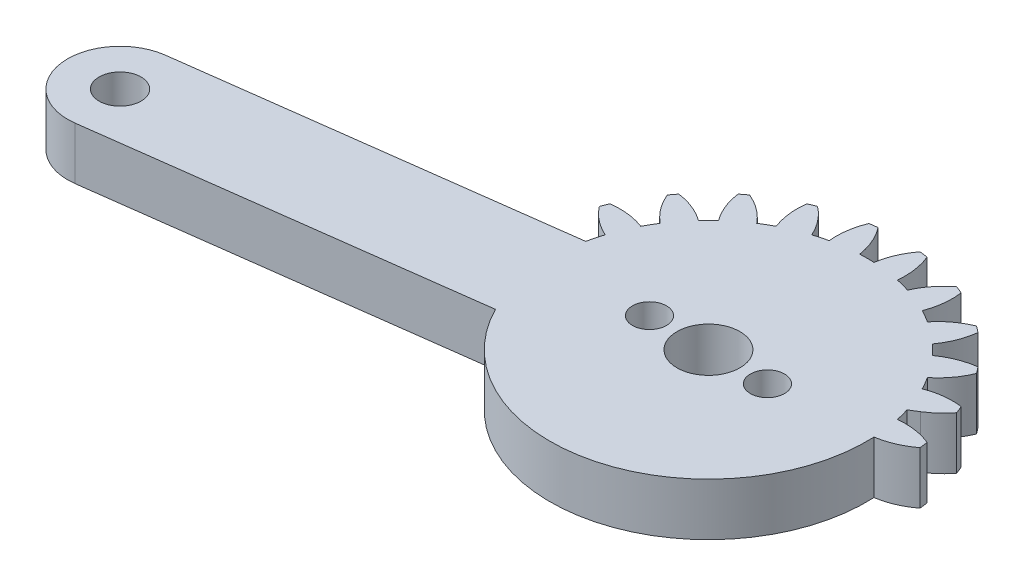
SolidWorks part; units mm, degrees
ref_plane "Front Plane" through (0, 0, 0) normal (0, 0, 1) x (1, 0, 0)
ref_plane "Top Plane" through (0, 0, 0) normal (0, 1, 0) x (1, 0, 0)
ref_plane "Right Plane" through (0, 0, 0) normal (1, 0, 0) x (0, 0, -1)
sketch "Sketch1" plane through (0, 0, 0) normal (0, 1, 0) x (1, 0, 0)
  line L0 (20.6437, 4) -> (2.0816, 4)
  line L1 (2.0816, -4) -> (20.6437, -4)
  arc A0 (2.0816, 4) -> (3.5217, 5.3071) centre (-0.7683, 8.5867) ccw
  arc A1 (3.5217, 5.3071) -> (3.2829, 5.8838) centre (-10.1063, 0) ccw
  arc A2 (3.2829, 5.8838) -> (0.6271, 5.5703) centre (2.5684, 0.5313) ccw
  arc A3 (0.6271, 5.5703) -> (0.0844, 6.5103) centre (-10.1063, 0) ccw
  arc A4 (0.0844, 6.5103) -> (1.6838, 8.6535) centre (-3.3089, 10.711) ccw
  arc A5 (1.6838, 8.6535) -> (1.3038, 9.1487) centre (-10.1063, 0) ccw
  arc A6 (1.3038, 9.1487) -> (-1.1803, 8.1585) centre (1.999, 3.7936) ccw
  arc A7 (-1.1803, 8.1585) -> (-1.9479, 8.926) centre (-10.1063, 0) ccw
  arc A8 (-1.9479, 8.926) -> (-0.9576, 11.4102) centre (-6.3127, 12.1053) ccw
  arc A9 (-0.9576, 11.4102) -> (-1.4528, 11.7901) centre (-10.1063, 0) ccw
  arc A10 (-1.4528, 11.7901) -> (-3.596, 10.1907) centre (0.6046, 6.7975) ccw
  arc A11 (-3.596, 10.1907) -> (-4.5361, 10.7334) centre (-10.1063, 0) ccw
  arc A12 (-4.5361, 10.7334) -> (-4.2225, 13.3892) centre (-9.5751, 12.6747) ccw
  arc A13 (-4.2225, 13.3892) -> (-4.7992, 13.6281) centre (-10.1063, 0) ccw
  arc A14 (-4.7992, 13.6281) -> (-6.4554, 11.5285) centre (-1.5196, 9.3381) ccw
  arc A15 (-6.4554, 11.5285) -> (-7.5039, 11.8094) centre (-10.1063, 0) ccw
  arc A16 (-7.5039, 11.8094) -> (-7.8884, 14.4558) centre (-12.8736, 12.3803) ccw
  arc A17 (-7.8884, 14.4558) -> (-8.5072, 14.5373) centre (-10.1063, 0) ccw
  arc A18 (-8.5072, 14.5373) -> (-9.5636, 12.0806) centre (-4.2291, 11.2423) ccw
  arc A19 (-9.5636, 12.0806) -> (-10.6491, 12.0806) centre (-10.1063, 0) ccw
  arc A20 (-10.6491, 12.0806) -> (-11.7054, 14.5373) centre (-15.9836, 11.2423) ccw
  arc A21 (-11.7054, 14.5373) -> (-12.3243, 14.4558) centre (-10.1063, 0) ccw
  arc A22 (-12.3243, 14.4558) -> (-12.7088, 11.8094) centre (-7.3391, 12.3803) ccw
  arc A23 (-12.7088, 11.8094) -> (-13.7573, 11.5285) centre (-10.1063, 0) ccw
  arc A24 (-13.7573, 11.5285) -> (-15.4135, 13.6281) centre (-18.6931, 9.3381) ccw
  arc A25 (-15.4135, 13.6281) -> (-15.9901, 13.3892) centre (-10.1063, 0) ccw
  arc A26 (-15.9901, 13.3892) -> (-15.6766, 10.7334) centre (-10.6376, 12.6747) ccw
  arc A27 (-15.6766, 10.7334) -> (-16.6166, 10.1907) centre (-10.1063, 0) ccw
  arc A28 (-16.6166, 10.1907) -> (-18.7599, 11.7901) centre (-20.8173, 6.7975) ccw
  arc A29 (-18.7599, 11.7901) -> (-19.255, 11.4102) centre (-10.1063, 0) ccw
  arc A30 (-19.255, 11.4102) -> (-18.2648, 8.926) centre (-13.9, 12.1053) ccw
  arc A31 (-18.2648, 8.926) -> (-19.0324, 8.1585) centre (-10.1063, 0) ccw
  arc A32 (-19.0324, 8.1585) -> (-21.5165, 9.1487) centre (-22.2117, 3.7936) ccw
  arc A33 (-21.5165, 9.1487) -> (-21.8965, 8.6535) centre (-10.1063, 0) ccw
  arc A34 (-21.8965, 8.6535) -> (-20.2971, 6.5103) centre (-16.9038, 10.711) ccw
  arc A35 (-20.2971, 6.5103) -> (-20.8398, 5.5703) centre (-10.1063, 0) ccw
  arc A36 (-20.8398, 5.5703) -> (-23.4956, 5.8838) centre (-22.7811, 0.5313) ccw
  arc A37 (-23.4956, 5.8838) -> (-23.7344, 5.3071) centre (-10.1063, 0) ccw
  arc A38 (-23.7344, 5.3071) -> (-21.6348, 3.6509) centre (-19.4444, 8.5867) ccw
  arc A39 (-21.6348, 3.6509) -> (-21.9157, 2.6025) centre (-10.1063, 0) ccw
  arc A40 (-21.9157, 2.6025) -> (-24.5622, 2.2179) centre (-22.4867, -2.7673) ccw
  arc A41 (-24.5622, 2.2179) -> (-24.6437, 1.5991) centre (-10.1063, 0) ccw
  arc A42 (-24.6437, 1.5991) -> (-22.1869, 0.5427) centre (-21.3486, 5.8773) ccw
  arc A43 (-22.1869, 0.5427) -> (-22.1869, -0.5427) centre (-10.1063, 0) ccw
  arc A44 (-22.1869, -0.5427) -> (-24.6437, -1.5991) centre (-21.3486, -5.8773) ccw
  arc A45 (-24.6437, -1.5991) -> (-24.5622, -2.2179) centre (-10.1063, 0) ccw
  arc A46 (-24.5622, -2.2179) -> (-21.9157, -2.6025) centre (-22.4867, 2.7673) ccw
  arc A47 (-21.9157, -2.6025) -> (-21.6348, -3.6509) centre (-10.1063, 0) ccw
  arc A48 (-21.6348, -3.6509) -> (-23.7344, -5.3071) centre (-19.4444, -8.5867) ccw
  arc A49 (-23.7344, -5.3071) -> (-23.4956, -5.8838) centre (-10.1063, 0) ccw
  arc A50 (-23.4956, -5.8838) -> (-20.8398, -5.5703) centre (-22.7811, -0.5313) ccw
  arc A51 (-20.8398, -5.5703) -> (-20.2971, -6.5103) centre (-10.1063, 0) ccw
  arc A52 (-20.2971, -6.5103) -> (-21.8965, -8.6535) centre (-16.9038, -10.711) ccw
  arc A53 (-21.8965, -8.6535) -> (-21.5165, -9.1487) centre (-10.1063, 0) ccw
  arc A54 (-21.5165, -9.1487) -> (-19.0324, -8.1585) centre (-22.2117, -3.7936) ccw
  arc A55 (-19.0324, -8.1585) -> (-18.2648, -8.926) centre (-10.1063, 0) ccw
  arc A56 (-18.2648, -8.926) -> (-19.255, -11.4102) centre (-13.9, -12.1053) ccw
  arc A57 (-19.255, -11.4102) -> (-18.7599, -11.7901) centre (-10.1063, 0) ccw
  arc A58 (-18.7599, -11.7901) -> (-16.6166, -10.1907) centre (-20.8173, -6.7975) ccw
  arc A59 (-16.6166, -10.1907) -> (-15.6766, -10.7334) centre (-10.1063, 0) ccw
  arc A60 (-15.6766, -10.7334) -> (-15.9901, -13.3892) centre (-10.6376, -12.6747) ccw
  arc A61 (-15.9901, -13.3892) -> (-15.4135, -13.6281) centre (-10.1063, 0) ccw
  arc A62 (-15.4135, -13.6281) -> (-13.7573, -11.5285) centre (-18.6931, -9.3381) ccw
  arc A63 (-13.7573, -11.5285) -> (-12.7088, -11.8094) centre (-10.1063, 0) ccw
  arc A64 (-12.7088, -11.8094) -> (-12.3243, -14.4558) centre (-7.3391, -12.3803) ccw
  arc A65 (-12.3243, -14.4558) -> (-11.7054, -14.5373) centre (-10.1063, 0) ccw
  arc A66 (-11.7054, -14.5373) -> (-10.6491, -12.0806) centre (-15.9836, -11.2423) ccw
  arc A67 (-10.6491, -12.0806) -> (-9.5636, -12.0806) centre (-10.1063, 0) ccw
  arc A68 (-9.5636, -12.0806) -> (-8.5072, -14.5373) centre (-4.2291, -11.2423) ccw
  arc A69 (-8.5072, -14.5373) -> (-7.8884, -14.4558) centre (-10.1063, 0) ccw
  arc A70 (-7.8884, -14.4558) -> (-7.5039, -11.8094) centre (-12.8736, -12.3803) ccw
  arc A71 (-7.5039, -11.8094) -> (-6.4554, -11.5285) centre (-10.1063, 0) ccw
  arc A72 (-6.4554, -11.5285) -> (-4.7992, -13.6281) centre (-1.5196, -9.3381) ccw
  arc A73 (-4.7992, -13.6281) -> (-4.2225, -13.3892) centre (-10.1063, 0) ccw
  arc A74 (-4.2225, -13.3892) -> (-4.5361, -10.7334) centre (-9.5751, -12.6747) ccw
  arc A75 (-4.5361, -10.7334) -> (-3.596, -10.1907) centre (-10.1063, 0) ccw
  arc A76 (-3.596, -10.1907) -> (-1.4528, -11.7901) centre (0.6046, -6.7975) ccw
  arc A77 (-1.4528, -11.7901) -> (-0.9576, -11.4102) centre (-10.1063, 0) ccw
  arc A78 (-0.9576, -11.4102) -> (-1.9479, -8.926) centre (-6.3127, -12.1053) ccw
  arc A79 (-1.9479, -8.926) -> (-1.1803, -8.1585) centre (-10.1063, 0) ccw
  arc A80 (-1.1803, -8.1585) -> (1.3038, -9.1487) centre (1.999, -3.7936) ccw
  arc A81 (1.3038, -9.1487) -> (1.6838, -8.6535) centre (-10.1063, 0) ccw
  arc A82 (1.6838, -8.6535) -> (0.0844, -6.5103) centre (-3.3089, -10.711) ccw
  arc A83 (0.0844, -6.5103) -> (0.6271, -5.5703) centre (-10.1063, 0) ccw
  arc A84 (0.6271, -5.5703) -> (3.2829, -5.8838) centre (2.5684, -0.5313) ccw
  arc A85 (3.2829, -5.8838) -> (3.5217, -5.3071) centre (-10.1063, 0) ccw
  arc A86 (3.5217, -5.3071) -> (2.0816, -4) centre (-0.7683, -8.5867) ccw
  arc A87 (20.6437, -4) -> (20.6437, 4) centre (20.6437, 0) ccw
  circle A88 centre (-10.1063, 0) radius 1.5
  circle A89 centre (20.6437, 0) radius 1.6
  dimension "D1" = 3
  dimension "D2" = 3.2
extrude "Boss-Extrude1" add sketch "Sketch1" along normal blind 4
sketch "Sketch3" plane through (0, 4, 0) normal (0, 1, 0) x (1, 0, 0)
  line L0 (-10.1063, 0) -> (-40.8563, 0) construction
  line L1 (-10.1063, 0) -> (-49.7641, -5.221)
  line L2 (-10.6284, 3.9658) -> (-50.2862, -1.2553)
  line L3 (-9.5842, -3.9658) -> (-49.242, -9.1868)
  line L4 (-10.1063, 0) -> (-4.5096, 13.5117) construction
  line L5 (-10.1063, 0) -> (-8.1974, 14.4999) construction
  circle A0 centre (-10.1063, 0) radius 1.5
  circle A1 centre (20.6437, 0) radius 1.6 construction
  circle A2 centre (20.6437, 0) radius 1.6
  circle A3 centre (-49.7641, -5.221) radius 1.6
  circle A4 centre (-49.7641, -5.221) radius 4
  circle A5 centre (-10.1063, 0) radius 4
  arc A6 (-4.2225, 13.3892) -> (-4.7992, 13.6281) centre (-10.1063, 0) ccw construction
  arc A7 (-7.8884, 14.4558) -> (-8.5072, 14.5373) centre (-10.1063, 0) ccw construction
  dimension "D2" = 3
  dimension "D5" = 3.2
  dimension "D6" = 8
  dimension "D7" = 8
  dimension "D1" = 40
  dimension "D4" = 7.5
extrude "Boss-Extrude2" add sketch "Sketch3" against normal blind 4
sketch "Sketch4" plane through (0, 4, 0) normal (0, 1, 0) x (1, 0, 0)
  line L0 (20.6437, 4) -> (2.0816, 4) construction
  line L1 (2.0816, -4) -> (20.6437, -4) construction
  line L2 (20.6437, 4) -> (2.0816, 4)
  line L3 (2.0816, -4) -> (20.6437, -4)
  line L4 (2.0816, 4) -> (1.4381, 3.6001)
  line L5 (-21.6245, -5.5509) -> (-20.8986, -5.4553)
  line L6 (-10.1063, 0) -> (0.0844, 6.5103) construction
  line L7 (-10.1063, 0) -> (1.9742, 0.5427) construction
  line L8 (-24.5755, 2.1296) -> (-50.2862, -1.2553)
  line L9 (-49.242, -9.1868) -> (-23.5312, -5.8019)
  line L10 (2.0816, -4) -> (20.6437, -4)
  line L11 (20.6437, 4) -> (2.0816, 4)
  line L12 (-21.9429, 2.4762) -> (-50.2862, -1.2553)
  line L13 (-49.242, -9.1868) -> (-21.6245, -5.5509)
  line L14 (2.0816, -4) -> (20.6437, -4)
  line L15 (20.6437, 4) -> (2.0816, 4)
  circle A0 centre (-10.1063, 0) radius 12.0927
  arc A1 (3.2829, 5.8838) -> (0.6271, 5.5703) centre (2.5684, 0.5313) ccw construction
  arc A2 (3.5217, 5.3071) -> (3.2829, 5.8838) centre (-10.1063, 0) ccw construction
  arc A3 (2.0816, 4) -> (3.5217, 5.3071) centre (-0.7683, 8.5867) ccw construction
  arc A4 (20.6437, -4) -> (20.6437, 4) centre (20.6437, 0) ccw construction
  arc A5 (3.5217, -5.3071) -> (2.0816, -4) centre (-0.7683, -8.5867) ccw construction
  arc A6 (3.2829, -5.8838) -> (3.5217, -5.3071) centre (-10.1063, 0) ccw construction
  arc A7 (0.6271, -5.5703) -> (3.2829, -5.8838) centre (2.5684, -0.5313) ccw construction
  arc A8 (3.2829, 5.8838) -> (0.6271, 5.5703) centre (2.5684, 0.5313) ccw
  arc A9 (3.5217, 5.3071) -> (3.2829, 5.8838) centre (-10.1063, 0) ccw
  arc A10 (2.0816, 4) -> (3.5217, 5.3071) centre (-0.7683, 8.5867) ccw
  arc A11 (20.6437, -4) -> (20.6437, 4) centre (20.6437, 0) ccw
  arc A12 (3.5217, -5.3071) -> (2.0816, -4) centre (-0.7683, -8.5867) ccw
  arc A13 (3.2829, -5.8838) -> (3.5217, -5.3071) centre (-10.1063, 0) ccw
  arc A14 (0.6271, -5.5703) -> (3.2829, -5.8838) centre (2.5684, -0.5313) ccw
  arc A15 (1.9742, 0.5427) -> (4.431, 1.5991) centre (1.1359, 5.8773) ccw
  arc A16 (4.3495, 2.2179) -> (1.7031, 2.6025) centre (2.274, -2.7673) ccw
  arc A17 (4.431, 1.5991) -> (4.3495, 2.2179) centre (-10.1063, 0) ccw
  arc A95 (-21.6348, 3.6509) -> (-21.9157, 2.6025) centre (-10.1063, 0) ccw
  arc A96 (-50.2862, -1.2553) -> (-49.242, -9.1868) centre (-49.7641, -5.221) ccw
  arc A97 (-20.2971, -6.5103) -> (-21.8965, -8.6535) centre (-16.9038, -10.711) ccw
  arc A98 (-21.8965, -8.6535) -> (-21.5165, -9.1487) centre (-10.1063, 0) ccw
  arc A99 (-21.5165, -9.1487) -> (-19.0324, -8.1585) centre (-22.2117, -3.7936) ccw
  arc A100 (-19.0324, -8.1585) -> (-18.2648, -8.926) centre (-10.1063, 0) ccw
  arc A101 (-18.2648, -8.926) -> (-19.255, -11.4102) centre (-13.9, -12.1053) ccw
  arc A102 (-19.255, -11.4102) -> (-18.7599, -11.7901) centre (-10.1063, 0) ccw
  arc A103 (-18.7599, -11.7901) -> (-16.6166, -10.1907) centre (-20.8173, -6.7975) ccw
  arc A104 (-16.6166, -10.1907) -> (-15.6766, -10.7334) centre (-10.1063, 0) ccw
  arc A105 (-15.6766, -10.7334) -> (-15.9901, -13.3892) centre (-10.6376, -12.6747) ccw
  arc A106 (-15.9901, -13.3892) -> (-15.4135, -13.6281) centre (-10.1063, 0) ccw
  arc A107 (-15.4135, -13.6281) -> (-13.7573, -11.5285) centre (-18.6931, -9.3381) ccw
  arc A108 (-13.7573, -11.5285) -> (-12.7088, -11.8094) centre (-10.1063, 0) ccw
  arc A109 (-12.7088, -11.8094) -> (-12.3243, -14.4558) centre (-7.3391, -12.3803) ccw
  arc A110 (-12.3243, -14.4558) -> (-11.7054, -14.5373) centre (-10.1063, 0) ccw
  arc A111 (-11.7054, -14.5373) -> (-10.6491, -12.0806) centre (-15.9836, -11.2423) ccw
  arc A112 (-10.6491, -12.0806) -> (-9.5636, -12.0806) centre (-10.1063, 0) ccw
  arc A113 (-9.5636, -12.0806) -> (-8.5072, -14.5373) centre (-4.2291, -11.2423) ccw
  arc A114 (-8.5072, -14.5373) -> (-7.8884, -14.4558) centre (-10.1063, 0) ccw
  arc A115 (-7.8884, -14.4558) -> (-7.5039, -11.8094) centre (-12.8736, -12.3803) ccw
  arc A116 (-7.5039, -11.8094) -> (-6.4554, -11.5285) centre (-10.1063, 0) ccw
  arc A117 (-6.4554, -11.5285) -> (-4.7992, -13.6281) centre (-1.5196, -9.3381) ccw
  arc A118 (-4.7992, -13.6281) -> (-4.2225, -13.3892) centre (-10.1063, 0) ccw
  arc A119 (-4.2225, -13.3892) -> (-4.5361, -10.7334) centre (-9.5751, -12.6747) ccw
  arc A120 (-4.5361, -10.7334) -> (-3.596, -10.1907) centre (-10.1063, 0) ccw
  arc A121 (-3.596, -10.1907) -> (-1.4528, -11.7901) centre (0.6046, -6.7975) ccw
  arc A122 (-1.4528, -11.7901) -> (-0.9576, -11.4102) centre (-10.1063, 0) ccw
  arc A123 (-0.9576, -11.4102) -> (-1.9479, -8.926) centre (-6.3127, -12.1053) ccw
  arc A124 (-1.9479, -8.926) -> (-1.1803, -8.1585) centre (-10.1063, 0) ccw
  arc A125 (-1.1803, -8.1585) -> (1.3038, -9.1487) centre (1.999, -3.7936) ccw
  arc A126 (1.3038, -9.1487) -> (1.6838, -8.6535) centre (-10.1063, 0) ccw
  arc A127 (1.6838, -8.6535) -> (0.0844, -6.5103) centre (-3.3089, -10.711) ccw
  arc A128 (0.0844, -6.5103) -> (0.6271, -5.5703) centre (-10.1063, 0) ccw
  arc A129 (0.6271, -5.5703) -> (3.2829, -5.8838) centre (2.5684, -0.5313) ccw
  arc A130 (3.2829, -5.8838) -> (3.5217, -5.3071) centre (-10.1063, 0) ccw
  arc A131 (3.5217, -5.3071) -> (2.0816, -4) centre (-0.7683, -8.5867) ccw
  arc A132 (20.6437, -4) -> (20.6437, 4) centre (20.6437, 0) ccw
  arc A133 (2.0816, 4) -> (3.5217, 5.3071) centre (-0.7683, 8.5867) ccw
  arc A134 (3.5217, 5.3071) -> (3.2829, 5.8838) centre (-10.1063, 0) ccw
  arc A135 (3.2829, 5.8838) -> (0.6271, 5.5703) centre (2.5684, 0.5313) ccw
  arc A136 (0.6271, 5.5703) -> (0.0844, 6.5103) centre (-10.1063, 0) ccw
  arc A137 (0.0844, 6.5103) -> (1.6838, 8.6535) centre (-3.3089, 10.711) ccw
  arc A138 (1.6838, 8.6535) -> (1.3038, 9.1487) centre (-10.1063, 0) ccw
  arc A139 (1.3038, 9.1487) -> (-1.1803, 8.1585) centre (1.999, 3.7936) ccw
  arc A140 (-1.1803, 8.1585) -> (-1.9479, 8.926) centre (-10.1063, 0) ccw
  arc A141 (-1.9479, 8.926) -> (-0.9576, 11.4102) centre (-6.3127, 12.1053) ccw
  arc A142 (-0.9576, 11.4102) -> (-1.4528, 11.7901) centre (-10.1063, 0) ccw
  arc A143 (-1.4528, 11.7901) -> (-3.596, 10.1907) centre (0.6046, 6.7975) ccw
  arc A144 (-3.596, 10.1907) -> (-4.5361, 10.7334) centre (-10.1063, 0) ccw
  arc A145 (-4.5361, 10.7334) -> (-4.2225, 13.3892) centre (-9.5751, 12.6747) ccw
  arc A146 (-4.2225, 13.3892) -> (-4.7992, 13.6281) centre (-10.1063, 0) ccw
  arc A147 (-4.7992, 13.6281) -> (-6.4554, 11.5285) centre (-1.5196, 9.3381) ccw
  arc A148 (-6.4554, 11.5285) -> (-7.5039, 11.8094) centre (-10.1063, 0) ccw
  arc A149 (-7.5039, 11.8094) -> (-7.8884, 14.4558) centre (-12.8736, 12.3803) ccw
  arc A150 (-7.8884, 14.4558) -> (-8.5072, 14.5373) centre (-10.1063, 0) ccw
  arc A151 (-8.5072, 14.5373) -> (-9.5636, 12.0806) centre (-4.2291, 11.2423) ccw
  arc A152 (-9.5636, 12.0806) -> (-10.6491, 12.0806) centre (-10.1063, 0) ccw
  arc A153 (-10.6491, 12.0806) -> (-11.7054, 14.5373) centre (-15.9836, 11.2423) ccw
  arc A154 (-11.7054, 14.5373) -> (-12.3243, 14.4558) centre (-10.1063, 0) ccw
  arc A155 (-12.3243, 14.4558) -> (-12.7088, 11.8094) centre (-7.3391, 12.3803) ccw
  arc A156 (-12.7088, 11.8094) -> (-13.7573, 11.5285) centre (-10.1063, 0) ccw
  arc A157 (-13.7573, 11.5285) -> (-15.4135, 13.6281) centre (-18.6931, 9.3381) ccw
  arc A158 (-15.4135, 13.6281) -> (-15.9901, 13.3892) centre (-10.1063, 0) ccw
  arc A159 (-15.9901, 13.3892) -> (-15.6766, 10.7334) centre (-10.6376, 12.6747) ccw
  arc A160 (-15.6766, 10.7334) -> (-16.6166, 10.1907) centre (-10.1063, 0) ccw
  arc A161 (-16.6166, 10.1907) -> (-18.7599, 11.7901) centre (-20.8173, 6.7975) ccw
  arc A162 (-18.7599, 11.7901) -> (-19.255, 11.4102) centre (-10.1063, 0) ccw
  arc A163 (-19.255, 11.4102) -> (-18.2648, 8.926) centre (-13.9, 12.1053) ccw
  arc A164 (-18.2648, 8.926) -> (-19.0324, 8.1585) centre (-10.1063, 0) ccw
  arc A165 (-19.0324, 8.1585) -> (-21.5165, 9.1487) centre (-22.2117, 3.7936) ccw
  arc A166 (-21.5165, 9.1487) -> (-21.8965, 8.6535) centre (-10.1063, 0) ccw
  arc A167 (-21.8965, 8.6535) -> (-20.2971, 6.5103) centre (-16.9038, 10.711) ccw
  arc A168 (-20.2971, 6.5103) -> (-20.8398, 5.5703) centre (-10.1063, 0) ccw
  arc A169 (-20.8398, 5.5703) -> (-23.4956, 5.8838) centre (-22.7811, 0.5313) ccw
  arc A170 (-23.4956, 5.8838) -> (-23.7344, 5.3071) centre (-10.1063, 0) ccw
  arc A171 (-23.7344, 5.3071) -> (-21.6348, 3.6509) centre (-19.4444, 8.5867) ccw
  arc A172 (-21.6348, 3.6509) -> (-21.9157, 2.6025) centre (-10.1063, 0) ccw
  arc A175 (-23.4956, -5.8838) -> (-20.8398, -5.5703) centre (-22.7811, -0.5313) ccw
  arc A176 (-50.2862, -1.2553) -> (-49.242, -9.1868) centre (-49.7641, -5.221) ccw
  arc A177 (-20.2971, -6.5103) -> (-21.8965, -8.6535) centre (-16.9038, -10.711) ccw
  arc A178 (-21.8965, -8.6535) -> (-21.5165, -9.1487) centre (-10.1063, 0) ccw
  arc A179 (-21.5165, -9.1487) -> (-19.0324, -8.1585) centre (-22.2117, -3.7936) ccw
  arc A180 (-19.0324, -8.1585) -> (-18.2648, -8.926) centre (-10.1063, 0) ccw
  arc A181 (-18.2648, -8.926) -> (-19.255, -11.4102) centre (-13.9, -12.1053) ccw
  arc A182 (-19.255, -11.4102) -> (-18.7599, -11.7901) centre (-10.1063, 0) ccw
  arc A183 (-18.7599, -11.7901) -> (-16.6166, -10.1907) centre (-20.8173, -6.7975) ccw
  arc A184 (-16.6166, -10.1907) -> (-15.6766, -10.7334) centre (-10.1063, 0) ccw
  arc A185 (-15.6766, -10.7334) -> (-15.9901, -13.3892) centre (-10.6376, -12.6747) ccw
  arc A186 (-15.9901, -13.3892) -> (-15.4135, -13.6281) centre (-10.1063, 0) ccw
  arc A187 (-15.4135, -13.6281) -> (-13.7573, -11.5285) centre (-18.6931, -9.3381) ccw
  arc A188 (-13.7573, -11.5285) -> (-12.7088, -11.8094) centre (-10.1063, 0) ccw
  arc A189 (-12.7088, -11.8094) -> (-12.3243, -14.4558) centre (-7.3391, -12.3803) ccw
  arc A190 (-12.3243, -14.4558) -> (-11.7054, -14.5373) centre (-10.1063, 0) ccw
  arc A191 (-11.7054, -14.5373) -> (-10.6491, -12.0806) centre (-15.9836, -11.2423) ccw
  arc A192 (-10.6491, -12.0806) -> (-9.5636, -12.0806) centre (-10.1063, 0) ccw
  arc A193 (-9.5636, -12.0806) -> (-8.5072, -14.5373) centre (-4.2291, -11.2423) ccw
  arc A194 (-8.5072, -14.5373) -> (-7.8884, -14.4558) centre (-10.1063, 0) ccw
  arc A195 (-7.8884, -14.4558) -> (-7.5039, -11.8094) centre (-12.8736, -12.3803) ccw
  arc A196 (-7.5039, -11.8094) -> (-6.4554, -11.5285) centre (-10.1063, 0) ccw
  arc A197 (-6.4554, -11.5285) -> (-4.7992, -13.6281) centre (-1.5196, -9.3381) ccw
  arc A198 (-4.7992, -13.6281) -> (-4.2225, -13.3892) centre (-10.1063, 0) ccw
  arc A199 (-4.2225, -13.3892) -> (-4.5361, -10.7334) centre (-9.5751, -12.6747) ccw
  arc A200 (-4.5361, -10.7334) -> (-3.596, -10.1907) centre (-10.1063, 0) ccw
  arc A201 (-3.596, -10.1907) -> (-1.4528, -11.7901) centre (0.6046, -6.7975) ccw
  arc A202 (-1.4528, -11.7901) -> (-0.9576, -11.4102) centre (-10.1063, 0) ccw
  arc A203 (-0.9576, -11.4102) -> (-1.9479, -8.926) centre (-6.3127, -12.1053) ccw
  arc A204 (-1.9479, -8.926) -> (-1.1803, -8.1585) centre (-10.1063, 0) ccw
  arc A205 (-1.1803, -8.1585) -> (1.3038, -9.1487) centre (1.999, -3.7936) ccw
  arc A206 (1.3038, -9.1487) -> (1.6838, -8.6535) centre (-10.1063, 0) ccw
  arc A207 (1.6838, -8.6535) -> (0.0844, -6.5103) centre (-3.3089, -10.711) ccw
  arc A208 (0.0844, -6.5103) -> (0.6271, -5.5703) centre (-10.1063, 0) ccw
  arc A209 (0.6271, -5.5703) -> (3.2829, -5.8838) centre (2.5684, -0.5313) ccw
  arc A210 (3.2829, -5.8838) -> (3.5217, -5.3071) centre (-10.1063, 0) ccw
  arc A211 (3.5217, -5.3071) -> (2.0816, -4) centre (-0.7683, -8.5867) ccw
  arc A212 (20.6437, -4) -> (20.6437, 4) centre (20.6437, 0) ccw
  arc A213 (2.0816, 4) -> (3.5217, 5.3071) centre (-0.7683, 8.5867) ccw
  arc A214 (3.5217, 5.3071) -> (3.2829, 5.8838) centre (-10.1063, 0) ccw
  arc A215 (3.2829, 5.8838) -> (0.6271, 5.5703) centre (2.5684, 0.5313) ccw
  arc A216 (0.6271, 5.5703) -> (0.0844, 6.5103) centre (-10.1063, 0) ccw
  arc A217 (0.0844, 6.5103) -> (1.6838, 8.6535) centre (-3.3089, 10.711) ccw
  arc A218 (1.6838, 8.6535) -> (1.3038, 9.1487) centre (-10.1063, 0) ccw
  arc A219 (1.3038, 9.1487) -> (-1.1803, 8.1585) centre (1.999, 3.7936) ccw
  arc A220 (-1.1803, 8.1585) -> (-1.9479, 8.926) centre (-10.1063, 0) ccw
  arc A221 (-1.9479, 8.926) -> (-0.9576, 11.4102) centre (-6.3127, 12.1053) ccw
  arc A222 (-0.9576, 11.4102) -> (-1.4528, 11.7901) centre (-10.1063, 0) ccw
  arc A223 (-1.4528, 11.7901) -> (-3.596, 10.1907) centre (0.6046, 6.7975) ccw
  arc A224 (-3.596, 10.1907) -> (-4.5361, 10.7334) centre (-10.1063, 0) ccw
  arc A225 (-4.5361, 10.7334) -> (-4.2225, 13.3892) centre (-9.5751, 12.6747) ccw
  arc A226 (-4.2225, 13.3892) -> (-4.7992, 13.6281) centre (-10.1063, 0) ccw
  arc A227 (-4.7992, 13.6281) -> (-6.4554, 11.5285) centre (-1.5196, 9.3381) ccw
  arc A228 (-6.4554, 11.5285) -> (-7.5039, 11.8094) centre (-10.1063, 0) ccw
  arc A229 (-7.5039, 11.8094) -> (-7.8884, 14.4558) centre (-12.8736, 12.3803) ccw
  arc A230 (-7.8884, 14.4558) -> (-8.5072, 14.5373) centre (-10.1063, 0) ccw
  arc A231 (-8.5072, 14.5373) -> (-9.5636, 12.0806) centre (-4.2291, 11.2423) ccw
  arc A232 (-9.5636, 12.0806) -> (-10.6491, 12.0806) centre (-10.1063, 0) ccw
  arc A233 (-10.6491, 12.0806) -> (-11.7054, 14.5373) centre (-15.9836, 11.2423) ccw
  arc A234 (-11.7054, 14.5373) -> (-12.3243, 14.4558) centre (-10.1063, 0) ccw
  arc A235 (-12.3243, 14.4558) -> (-12.7088, 11.8094) centre (-7.3391, 12.3803) ccw
  arc A236 (-12.7088, 11.8094) -> (-13.7573, 11.5285) centre (-10.1063, 0) ccw
  arc A237 (-13.7573, 11.5285) -> (-15.4135, 13.6281) centre (-18.6931, 9.3381) ccw
  arc A238 (-15.4135, 13.6281) -> (-15.9901, 13.3892) centre (-10.1063, 0) ccw
  arc A239 (-15.9901, 13.3892) -> (-15.6766, 10.7334) centre (-10.6376, 12.6747) ccw
  arc A240 (-15.6766, 10.7334) -> (-16.6166, 10.1907) centre (-10.1063, 0) ccw
  arc A241 (-16.6166, 10.1907) -> (-18.7599, 11.7901) centre (-20.8173, 6.7975) ccw
  arc A242 (-18.7599, 11.7901) -> (-19.255, 11.4102) centre (-10.1063, 0) ccw
  arc A243 (-19.255, 11.4102) -> (-18.2648, 8.926) centre (-13.9, 12.1053) ccw
  arc A244 (-18.2648, 8.926) -> (-19.0324, 8.1585) centre (-10.1063, 0) ccw
  arc A245 (-19.0324, 8.1585) -> (-21.5165, 9.1487) centre (-22.2117, 3.7936) ccw
  arc A246 (-21.5165, 9.1487) -> (-21.8965, 8.6535) centre (-10.1063, 0) ccw
  arc A247 (-21.8965, 8.6535) -> (-20.2971, 6.5103) centre (-16.9038, 10.711) ccw
  arc A248 (-20.2971, 6.5103) -> (-20.8398, 5.5703) centre (-10.1063, 0) ccw
  arc A249 (-20.8398, 5.5703) -> (-23.4956, 5.8838) centre (-22.7811, 0.5313) ccw
  arc A250 (-23.4956, 5.8838) -> (-23.7344, 5.3071) centre (-10.1063, 0) ccw
  arc A251 (-23.7344, 5.3071) -> (-21.6348, 3.6509) centre (-19.4444, 8.5867) ccw
  arc A252 (-23.4956, -5.8838) -> (-20.8398, -5.5703) centre (-22.7811, -0.5313) ccw
  arc A253 (-20.8398, -5.5703) -> (-20.2971, -6.5103) centre (-10.1063, 0) ccw
  arc A254 (-20.8398, -5.5703) -> (-20.2971, -6.5103) centre (-10.1063, 0) ccw
  arc A255 (-23.5312, -5.8019) -> (-23.4956, -5.8838) centre (-10.1063, 0) ccw
  arc A256 (-23.5312, -5.8019) -> (-23.4956, -5.8838) centre (-10.1063, 0) ccw
  arc A257 (-21.9157, 2.6025) -> (-24.5622, 2.2179) centre (-22.4867, -2.7673) ccw
  arc A258 (-21.9157, 2.6025) -> (-24.5622, 2.2179) centre (-22.4867, -2.7673) ccw
  arc A259 (-24.5622, 2.2179) -> (-24.5755, 2.1296) centre (-10.1063, 0) ccw
  arc A260 (-24.5622, 2.2179) -> (-24.5755, 2.1296) centre (-10.1063, 0) ccw
  point P40 (-10.1063, 0)
  dimension "D2" = 24.1855
  dimension "D4" = 30
  dimension "D1" = 0
  dimension "D3" = 2
extrude "Cut-Extrude1" cut sketch "Sketch4" against normal blind 4 contours A178 A179 A0 L5 A177 | A182 A183 A0 A181 | A186 A187 A0 A185 | A190 A191 A0 A189 | A194 A195 A0 A193 | A198 A199 A0 A197 | A202 A203 A0 A201 | A206 A207 A0 A205 | A258 A260 L12 A0 | L13 A256 A252 A0 L5 | A0 A14 A13 A12 L3 A11 L2 L4
sketch "Sketch5" plane through (0, 4, 0) normal (0, 1, 0) x (1, 0, 0)
  circle A0 centre (-10.1063, 0) radius 2.4
  circle A1 centre (-5.6063, 0) radius 1.3
  circle A2 centre (-14.6063, 0) radius 1.3
  circle A3 centre (-10.1063, 0) radius 1.5 construction
  dimension "D1" = 4.8
  dimension "D2" = 2.6
  dimension "D3" = 2.6
  dimension "D4" = 4.5
  dimension "D5" = 9
extrude "Cut-Extrude2" cut sketch "Sketch5" against normal up to next contours A2 | A1 | A0
